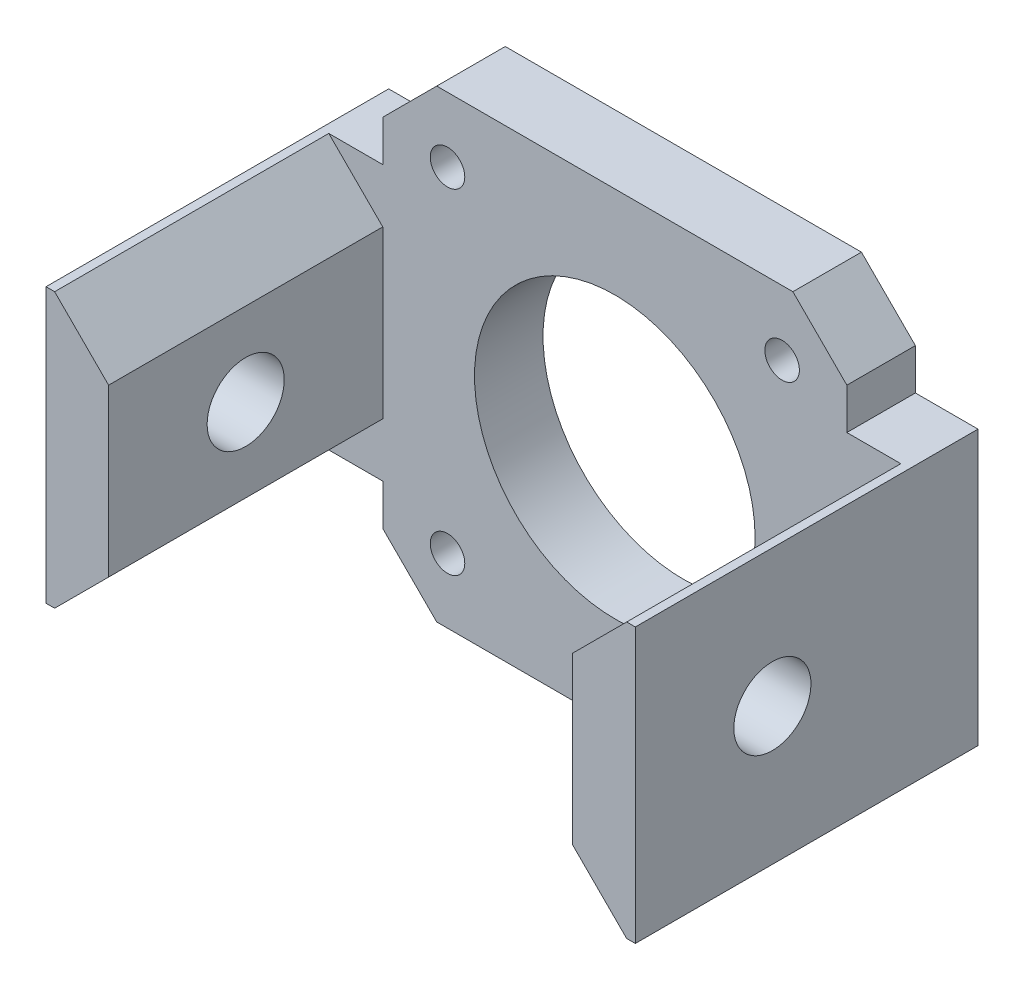
SolidWorks part; units mm, degrees
ref_plane "Front Plane" through (0, 0, 0) normal (0, 0, 1) x (1, 0, 0)
ref_plane "Top Plane" through (0, 0, 0) normal (0, 1, 0) x (1, 0, 0)
ref_plane "Right Plane" through (0, 0, 0) normal (1, 0, 0) x (0, 0, -1)
sketch "Sketch1" plane through (0, 0, 0) normal (0, 0, 1) x (1, 0, 0)
  line L0 (9.1924, -9.1924) -> (-9.1924, 9.1924) construction
  line L1 (-14.3686, -14.3686) -> (14.3686, 14.3686) construction
  line L2 (-13, 0) -> (13, 0) construction
  line L3 (-9.1924, 9.1924) -> (-15.5, 15.5) construction
  line L4 (9.1924, -9.1924) -> (16.6314, -16.6314) construction
  line L5 (14.3686, 14.3686) -> (16.6314, 16.6314) construction
  line L6 (-14.3686, -14.3686) -> (-16.6314, -16.6314) construction
  line L8 (-21.5, 21.5) -> (21.5, 21.5)
  line L9 (-21.5, 21.5) -> (-21.5, -21.5) construction
  line L10 (-21.5, -21.5) -> (21.5, -21.5)
  line L11 (21.5, 21.5) -> (21.5, -21.5) construction
  line L12 (-21.5, 21.5) -> (21.5, -21.5) construction
  line L13 (-21.5, -21.5) -> (21.5, 21.5) construction
  line L14 (-21.5, 21.5) -> (-27.3, 21.5)
  line L16 (-21.5, -21.5) -> (-27.3, -21.5)
  line L17 (-27.3, 21.5) -> (-27.3, -21.5)
  line L18 (-21.5, 21.5) -> (-27.3, -21.5) construction
  line L19 (-21.5, -21.5) -> (-27.3, 21.5) construction
  line L20 (21.5, -21.5) -> (27.3, -21.5)
  line L22 (21.5, 21.5) -> (27.3, 21.5)
  line L23 (27.3, -21.5) -> (27.3, 21.5)
  line L24 (21.5, -21.5) -> (27.3, 21.5) construction
  line L25 (21.5, 21.5) -> (27.3, -21.5) construction
  circle A0 centre (0, 0) radius 13
  circle A1 centre (-15.5, 15.5) radius 1.6
  circle A2 centre (15.5, 15.5) radius 1.6
  circle A3 centre (15.5, -15.5) radius 1.6
  circle A4 centre (-15.5, -15.5) radius 1.6
  point P23 (0, 0)
  point P27 (-24.4, 0)
  point P30 (24.4, 0)
  dimension "D1" = 26
  dimension "D4" = 3.2
  dimension "D2" = 45
  dimension "D3" = 90
  dimension "D5" = 31
  dimension "D6" = 43
  dimension "D7" = 43
  dimension "D8" = 5.8
  dimension "D9" = 5.8
extrude "Boss-Extrude1" add sketch "Sketch1" along normal blind 6.35
sketch "Sketch2" plane through (0, 0, 6.35) normal (0, 0, 1) x (1, 0, 0)
  line L0 (-27.3, 21.5) -> (-21.5, 21.5)
  line L1 (27.3, 21.5) -> (-27.3, 21.5) construction
  line L2 (-21.5, 21.5) -> (-21.5, -21.5)
  line L3 (-27.3, -21.5) -> (27.3, -21.5) construction
  line L4 (-21.5, -21.5) -> (-27.3, -21.5)
  line L5 (-27.3, -21.5) -> (-27.3, 21.5)
  line L6 (27.3, 21.5) -> (27.3, -21.5)
  line L7 (27.3, -21.5) -> (21.5, -21.5)
  line L8 (21.5, -21.5) -> (21.5, 21.5)
  line L9 (21.5, 21.5) -> (27.3, 21.5)
  dimension "D1" = 5.8
  dimension "D2" = 5.8
extrude "Boss-Extrude2" add sketch "Sketch2" along normal blind 25.4
sketch "Sketch4" plane through (0, 0, 6.35) normal (0, 0, 1) x (1, 0, 0)
  line L0 (-27.3, 0) -> (27.3, 0) construction
  line L1 (-27.3, 21.5) -> (-27.3, -21.5) construction
  line L2 (27.3, -21.5) -> (27.3, 21.5) construction
  line L3 (-27.3, 12.7) -> (-21.5, 12.7)
  line L5 (0, -21.5) -> (0, 21.5) construction
  line L6 (-21.5, 21.5) -> (-16.5, 21.5)
  line L7 (21.5, 21.5) -> (-21.5, 21.5) construction
  line L9 (-21.5, -21.5) -> (-21.5, 21.5) construction
  line L10 (-21.5, 16.5) -> (-16.5, 21.5)
  line L11 (-21.5, 16.5) -> (-21.5, 12.7)
  line L12 (-21.5, -21.5) -> (-21.5, 21.5) construction
  line L13 (-27.3, 21.5) -> (-21.5, 21.5)
  line L14 (-27.3, 21.5) -> (-27.3, 12.7)
  line L15 (-21.5, -21.5) -> (21.5, -21.5) construction
  line L16 (21.5, 21.5) -> (16.5, 21.5)
  line L17 (21.5, 16.5) -> (16.5, 21.5)
  line L18 (21.5, 16.5) -> (21.5, 12.7)
  line L19 (27.3, 12.7) -> (21.5, 12.7)
  line L20 (27.3, 21.5) -> (27.3, 12.7)
  line L21 (27.3, 21.5) -> (21.5, 21.5)
  line L22 (27.3, -21.5) -> (27.3, -12.7)
  line L23 (27.3, -12.7) -> (21.5, -12.7)
  line L24 (21.5, -16.5) -> (21.5, -12.7)
  line L25 (27.3, -21.5) -> (21.5, -21.5)
  line L26 (21.5, -16.5) -> (16.5, -21.5)
  line L27 (21.5, -21.5) -> (16.5, -21.5)
  line L28 (-27.3, -21.5) -> (-21.5, -21.5)
  line L29 (-21.5, -21.5) -> (-16.5, -21.5)
  line L30 (-21.5, -16.5) -> (-16.5, -21.5)
  line L31 (-21.5, -16.5) -> (-21.5, -12.7)
  line L32 (-27.3, -12.7) -> (-21.5, -12.7)
  line L33 (-27.3, -21.5) -> (-27.3, -12.7)
  line M22 (-21.5, -21.5) -> (21.5, -21.5)
  line M25 (-21.5, 21.5) -> (-21.5, -21.5)
  dimension "D1" = 12.7
  dimension "D3" = 5
  dimension "D4" = 5
extrude "Cut-Extrude1" cut sketch "Sketch4" against normal through all both and the other way through all contours L30 M25 M22 | L10 L6 L13 L14 L3 L11 | L22 L23 L24 L26 L27 L25 | L20 L19 L18 L17 L16 L21
sketch "Sketch5" plane through (-21.5, 0, 0) normal (1, 0, 0) x (0, 0, -1)
  line L0 (-19.05, 12.7) -> (-19.05, -12.7) construction
  line L1 (-6.35, 12.7) -> (-31.75, 12.7) construction
  line L2 (-6.35, -12.7) -> (-31.75, -12.7) construction
  line L3 (-31.75, 0) -> (-6.35, 0) construction
  line L4 (-31.75, -12.7) -> (-31.75, 12.7) construction
  line L5 (-6.35, -12.7) -> (-6.35, 12.7) construction
  circle A0 centre (-19.05, 0) radius 3.5719
  dimension "D1" = 7.1437
extrude "Cut-Extrude2" cut sketch "Sketch5" against normal through all both and the other way through all
chamfer "Chamfer1" distance 5 angle 45 4 edges at (21.5, -12.7, 19.05) (21.5, 12.7, 19.05) (-21.5, -12.7, 19.05) (-21.5, 12.7, 19.05)
ref_plane "Plane1" through (0, 0, 0) normal (0, 0, -1) x (-1, 0, 0)
